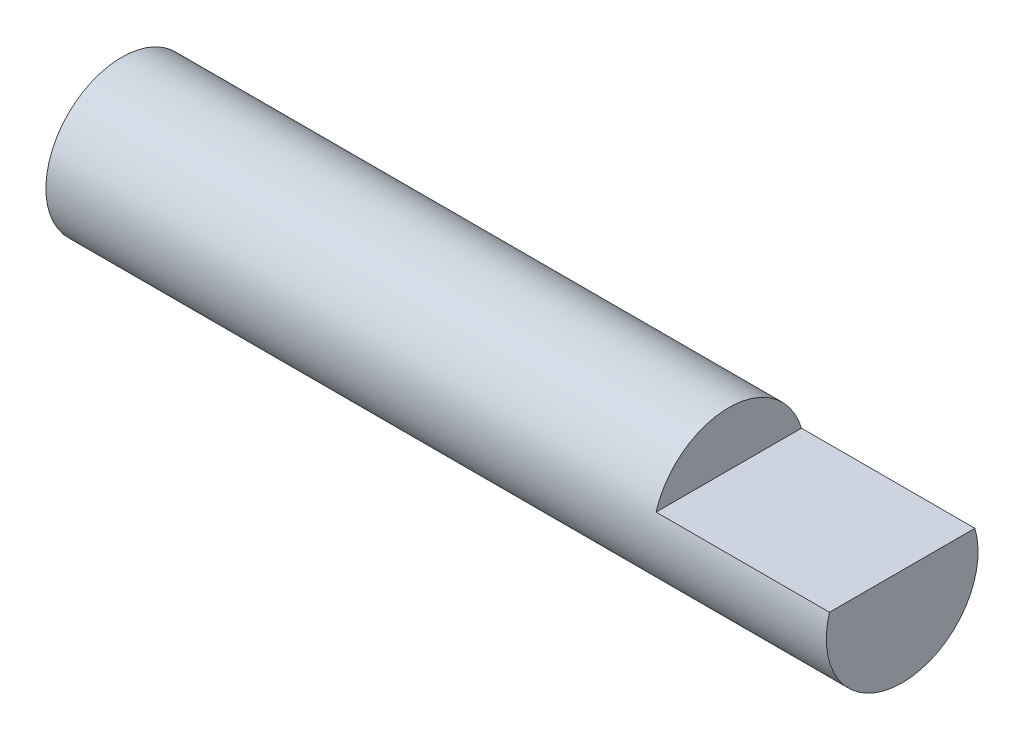
SolidWorks part; units mm, degrees
material "3003 Alloy"
ref_plane "Front" through (0, 0, 0) normal (0, 0, 1) x (1, 0, 0)
ref_plane "Top" through (0, 0, 0) normal (0, 1, 0) x (1, 0, 0)
ref_plane "Right" through (0, 0, 0) normal (1, 0, 0) x (0, 0, -1)
sketch "Sketch1" plane through (0, 0, 0) normal (1, 0, 0) x (0, 0, -1)
  circle A0 centre (0, 0) radius 5.5562
  dimension "D1" = 11.1125
extrude "Base-Extrude" add sketch "Sketch1" along normal blind 57.15
sketch "Sketch2" plane through (57.15, 0, 0) normal (1, 0, 0) x (0, 0, -1)
  line L0 (-5.3246, 1.5875) -> (5.3246, 1.5875)
  circle A0 centre (0, 0) radius 5.5562 construction
  arc A1 (5.3246, 1.5875) -> (-5.3246, 1.5875) centre (0, 0) ccw
  dimension "D1" = 1.5875
extrude "Cut-Extrude1" cut sketch "Sketch2" against normal blind 12.7
